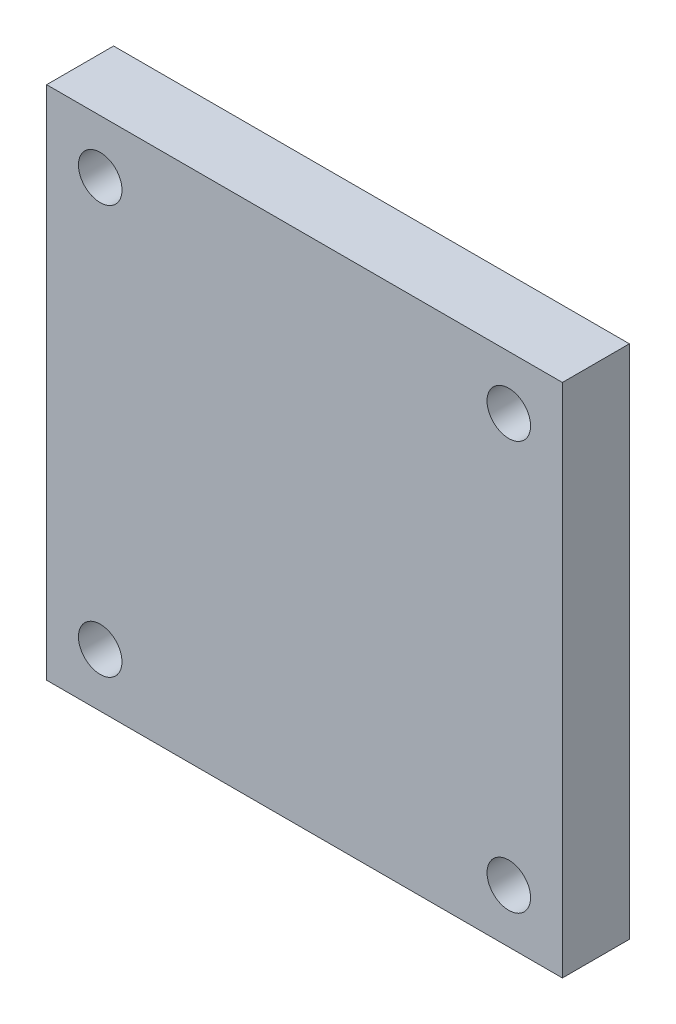
SolidWorks part; units mm, degrees
material "Plain Carbon Steel"
ref_plane "Front Plane" through (0, 0, 0) normal (0, 0, 1) x (1, 0, 0)
ref_plane "Top Plane" through (0, 0, 0) normal (0, 1, 0) x (1, 0, 0)
ref_plane "Right Plane" through (0, 0, 0) normal (1, 0, 0) x (0, 0, -1)
sketch "Sketch1" plane through (0, 0, 0) normal (0, 0, 1) x (1, 0, 0)
  line L0 (-77, -77) -> (77, -77)
  line L1 (-77, -77) -> (-77, 77)
  line L2 (77, -77) -> (77, 77)
  line L3 (-77, 77) -> (77, 77)
  line L4 (-77, -77) -> (77, 77) construction
  line L5 (77, -77) -> (-77, 77) construction
  line L6 (-77, 0) -> (77, 0) construction
  line L7 (0, 77) -> (0, -77) construction
  circle A0 centre (-61, 61) radius 6.5
  circle A1 centre (61, 61) radius 6.5
  circle A2 centre (-61, -61) radius 6.5
  circle A3 centre (61, -61) radius 6.5
  point P1 (0, 0)
  dimension "D3" = 13
  dimension "D5" = 16
  dimension "D1" = 154
  dimension "D2" = 16
  dimension "D4" = 154
extrude "Boss-Extrude1" add sketch "Sketch1" along normal mid plane 20
